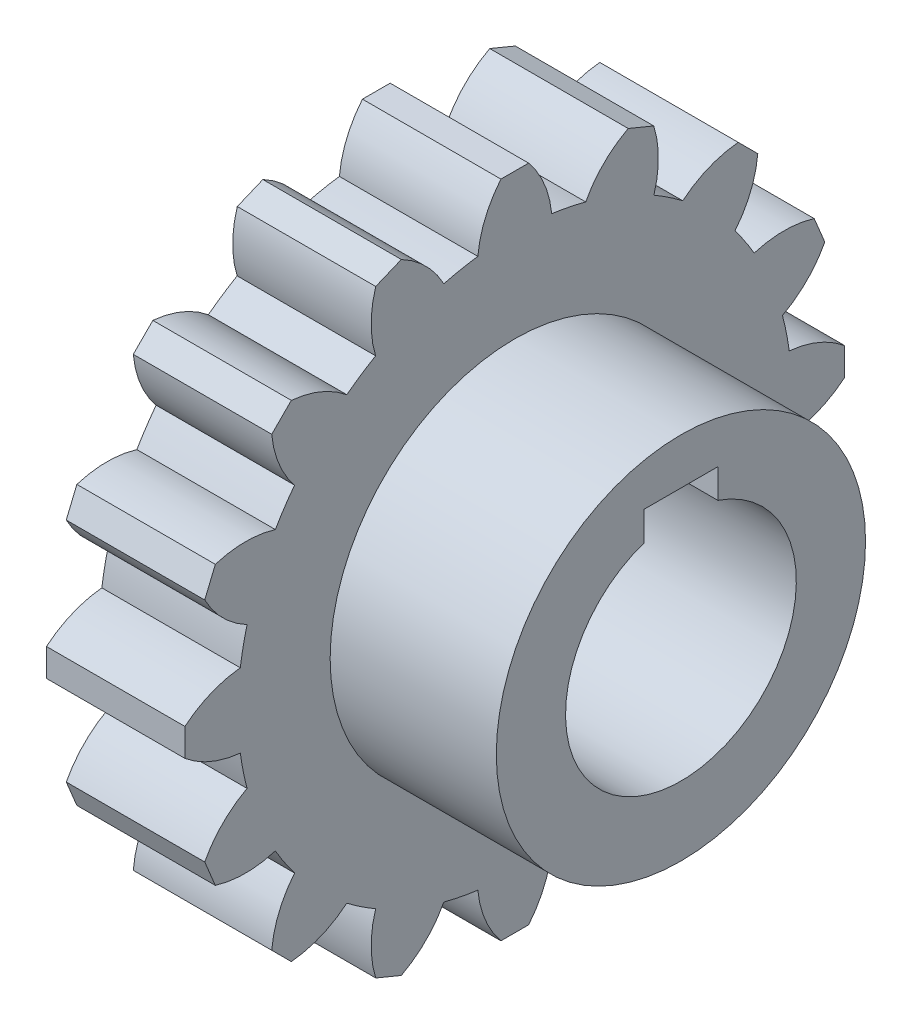
SolidWorks part; units mm, degrees
ref_plane "Front Plane" through (0, 0, 0) normal (0, 0, 1) x (1, 0, 0)
ref_plane "Top Plane" through (0, 0, 0) normal (0, 1, 0) x (1, 0, 0)
ref_plane "Right Plane" through (0, 0, 0) normal (1, 0, 0) x (0, 0, -1)
sketch "Sketch1" plane through (0, 0, 0) normal (1, 0, 0) x (0, 0, -1)
  circle A0 centre (0, 0) radius 30
  dimension "D1" = 60
extrude "Boss-Extrude1" add sketch "Sketch1" along normal mid plane 15
sketch "Sketch2" plane through (7.5, 0, 0) normal (1, 0, 0) x (0, 0, -1)
  line L0 (0, 0) -> (0, 39.3463) construction
  line L1 (-1.5, 35.7321) -> (1.5, 35.7321)
  arc A0 (-4, 29.7321) -> (4, 29.7321) centre (0, 0) cw
  circle A1 centre (0, 0) radius 30 construction
  arc A2 (1.5, 35.7321) -> (4, 29.7321) centre (-6.9505, 28.6902) cw
  arc A3 (-1.5, 35.7321) -> (-4, 29.7321) centre (6.9505, 28.6902) ccw
  point P6 (0, 35.7321)
  dimension "D5" = 11
  dimension "D1" = 3
  dimension "D3" = 4
  dimension "D4" = 6
extrude "Boss-Extrude2" add sketch "Sketch2" against normal through all
pattern_circular "CirPattern1" count 16 over 360 about axis through (0, 0, 0) along (1, 0, 0) of "Boss-Extrude2"
sketch "Sketch3" plane through (7.5, 0, 0) normal (1, 0, 0) x (0, 0, -1)
  circle A0 centre (0, 0) radius 20
  dimension "D1" = 40
extrude "Boss-Extrude3" add sketch "Sketch3" along normal mid plane 36
sketch "Sketch4" plane through (25.5, 0, 0) normal (1, 0, 0) x (0, 0, -1)
  line L0 (0, 0) -> (0, 15.945) construction
  line L2 (-4, 15) -> (4, 15)
  line L3 (-4, 15) -> (-4, 11.8427)
  line L5 (4, 15) -> (4, 11.8427)
  line L6 (-4, 15) -> (0, 12.5) construction
  line L7 (0, 12.5) -> (4, 15) construction
  arc A0 (-4, 11.8427) -> (4, 11.8427) centre (0, 0) ccw
  point P3 (0, 12.5)
  dimension "D1" = 12.5
  dimension "D2" = 15
  dimension "D3" = 8
  dimension "D4" = 4
extrude "Cut-Extrude1" cut sketch "Sketch4" against normal blind 44
